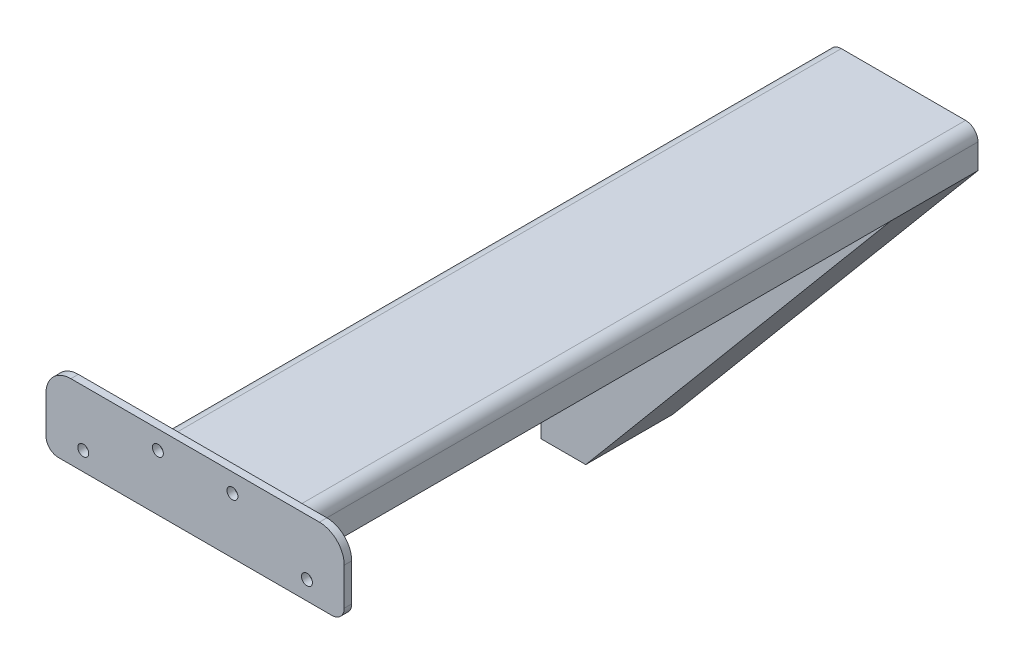
SolidWorks part; units mm, degrees
ref_plane "Front Plane" through (0, 0, 0) normal (0, 0, 1) x (1, 0, 0)
ref_plane "Top Plane" through (0, 0, 0) normal (0, 1, 0) x (1, 0, 0)
ref_plane "Right Plane" through (0, 0, 0) normal (1, 0, 0) x (0, 0, -1)
sketch "Sketch1" plane through (0, 0, 0) normal (0, 0, 1) x (1, 0, 0)
  line L23 (39.2356, -231.8935) -> (39.2356, -281.8935)
  line L24 (124.2987, -130.5192) -> (39.2356, -231.8935)
  line L25 (57.2806, -281.8935) -> (184.2987, -130.5192)
  line L26 (184.2987, -130.5192) -> (124.2987, -130.5192)
  line L27 (39.2356, -281.8935) -> (57.2806, -281.8935)
extrude "Boss-Extrude1" add sketch "Sketch1" along normal blind 35
sketch "Sketch5" plane through (0, -130.5192, 0) normal (0, 1, 0) x (1, 0, 0)
  line L0 (124.2987, -35) -> (39.2356, -35) construction
  line L1 (124.2987, 0) -> (84.2987, 0)
  line L2 (124.2987, 0) -> (124.2987, -35)
  line L3 (124.2987, -35) -> (84.2987, -35)
  line L4 (84.2987, 0) -> (84.2987, -35)
  line L5 (184.2987, 0) -> (184.2987, -35)
  line L6 (184.2987, 0) -> (204.2987, 0)
  line L10 (184.2987, -35) -> (204.2987, -35)
  line L11 (204.2987, -35) -> (204.2987, 0)
  dimension "D1" = 20
  dimension "D2" = 40
extrude "Boss-Extrude4" add sketch "Sketch5" against normal blind 5
sketch "Sketch6" plane through (0, 0, 35) normal (0, 0, 1) x (1, 0, 0)
  line L4 (184.2987, -130.5192) -> (184.2987, -135.5192)
  line L5 (184.2987, -135.5192) -> (180.1032, -135.5192)
  line L6 (57.2806, -281.8935) -> (184.2987, -130.5192) construction
  line L7 (180.1032, -135.5192) -> (184.2987, -130.5192)
extrude "Boss-Extrude5" add sketch "Sketch6" against normal blind 35
sketch "Sketch7" plane through (39.2356, 0, 0) normal (-1, 0, 0) x (0, 0, 1)
  line L0 (0, -231.8935) -> (35, -281.8935)
  line L6 (0, -231.8935) -> (35, -231.8935)
  line L22 (0, -231.8935) -> (0, -281.8935)
  line L23 (0, -281.8935) -> (35, -281.8935)
  line L24 (35, -231.8935) -> (35, -281.8935)
  line L25 (0, -281.8935) -> (35, -231.8935)
  line L27 (21.9741, -266.9425) -> (25.6746, -264.2539)
  line L28 (25.6746, -264.2539) -> (27.9616, -260.2927)
  line L29 (27.9616, -260.2927) -> (28.4397, -255.7437)
  line L30 (28.4397, -255.7437) -> (27.0263, -251.3935)
  line L31 (27.0263, -251.3935) -> (23.9656, -247.9943)
  line L32 (23.9656, -247.9943) -> (19.787, -246.1339)
  line L33 (19.787, -246.1339) -> (15.213, -246.1339)
  line L34 (15.213, -246.1339) -> (11.0344, -247.9943)
  line L35 (11.0344, -247.9943) -> (7.9737, -251.3935)
  line L36 (7.9737, -251.3935) -> (6.5603, -255.7437)
  line L37 (6.5603, -255.7437) -> (7.0384, -260.2927)
  line L38 (7.0384, -260.2927) -> (9.3254, -264.2539)
  line L39 (9.3254, -264.2539) -> (13.0259, -266.9425)
  line L40 (13.0259, -266.9425) -> (17.5, -267.8935)
  line L41 (17.5, -267.8935) -> (21.9741, -266.9425)
  circle A0 centre (17.5, -256.8935) radius 10.7596 construction
  dimension "D1" = 11
extrude "Cut-Extrude2" cut sketch "Sketch7" against normal blind 15
sketch "Sketch8" plane through (0, -135.5192, 0) normal (0, -1, 0) x (1, 0, 0)
  line L6 (180.1032, 35) -> (204.2987, 0)
  line L15 (84.2987, 35) -> (120.1032, 35)
  line L16 (84.2987, 35) -> (84.2987, 0)
  line L17 (84.2987, 0) -> (120.1032, 0)
  line L18 (120.1032, 35) -> (120.1032, 0)
  line L19 (180.1032, 35) -> (204.2987, 35)
  line L20 (180.1032, 35) -> (180.1032, 0)
  line L21 (180.1032, 0) -> (204.2987, 0)
  line L22 (204.2987, 35) -> (204.2987, 0)
  line L23 (204.2987, 35) -> (180.1032, 0)
  line L24 (84.2987, 35) -> (120.1032, 0)
  line L25 (120.1032, 35) -> (84.2987, 0)
  circle A4 centre (102.2009, 17.5) radius 2.15
  circle A5 centre (192.2009, 17.5) radius 2.15
  dimension "D1" = 4.3
  dimension "D2" = 4.3
extrude "Cut-Extrude3" cut sketch "Sketch8" against normal blind 10 contours L25 A4 L24 | L24 A4 L25 | L25 A4 L24 | L24 A4 L25 | L6 A5 L23 | L6 A5 L23 | L23 A5 L6 | L23 A5 L6
sketch "Sketch9" plane through (0, 0, 0) normal (0, 0, -1) x (-1, 0, 0)
  line L0 (-180.1032, -135.5192) -> (-180.1032, -120.5192)
  line L1 (-180.1032, -135.5192) -> (-120.1032, -135.5192)
  line L2 (-120.1032, -135.5192) -> (-120.1032, -120.5192)
  line L3 (-120.1032, -120.5192) -> (-180.1032, -120.5192)
  dimension "D1" = 15
extrude "Boss-Extrude6" add sketch "Sketch9" against normal blind 285
sketch "Sketch10" plane through (180.1032, 0, 0) normal (1, 0, 0) x (0, 0, -1)
  line L1 (-35, -130.5192) -> (0, -130.5192)
  line L2 (-35, -130.5192) -> (-35, -135.5192)
  line L3 (-35, -135.5192) -> (0, -135.5192)
  line L4 (0, -130.5192) -> (0, -135.5192)
extrude "Cut-Extrude4" cut sketch "Sketch10" along normal blind 250
sketch "Sketch11" plane through (120.1032, 0, 0) normal (-1, 0, 0) x (0, 0, 1)
  line L1 (0, -130.5192) -> (35, -130.5192)
  line L2 (0, -130.5192) -> (0, -135.5192)
  line L3 (0, -135.5192) -> (35, -135.5192)
  line L4 (35, -130.5192) -> (35, -135.5192)
extrude "Cut-Extrude5" cut sketch "Sketch11" along normal blind 250
sketch "Sketch12" plane through (0, 0, 285) normal (0, 0, 1) x (1, 0, 0)
  line L9 (120.1032, -120.5192) -> (90.1032, -120.5192)
  line L10 (120.1032, -120.5192) -> (120.1032, -135.5192)
  line L11 (120.1032, -135.5192) -> (90.1032, -135.5192)
  line L12 (90.1032, -120.5192) -> (90.1032, -135.5192)
  line L13 (180.1032, -120.5192) -> (210.1032, -120.5192)
  line L14 (180.1032, -120.5192) -> (180.1032, -135.5192)
  line L15 (180.1032, -135.5192) -> (210.1032, -135.5192)
  line L16 (210.1032, -120.5192) -> (210.1032, -135.5192)
  dimension "D1" = 30
  dimension "D2" = 30
extrude "Boss-Extrude7" add sketch "Sketch12" against normal blind 3
fillet "Fillet1" radius 5 1 edges at (120.1032, -135.5192, 17.5)
fillet "Fillet2" radius 5 2 edges at (180.1032, -120.5192, 141) (120.1032, -120.5192, 141)
sketch "Sketch13" plane through (0, 0, 282) normal (0, 0, -1) x (-1, 0, 0)
  line L0 (-180.1032, -135.5192) -> (-180.1032, -120.5192)
  line L1 (-210.1032, -120.5192) -> (-175.1032, -120.5192) construction
  line L2 (-210.1032, -120.5192) -> (-180.1032, -120.5192)
  line L3 (-120.1032, -135.5192) -> (-120.1032, -120.5192)
  line L4 (-125.1032, -120.5192) -> (-90.1032, -120.5192) construction
  line L5 (-120.1032, -120.5192) -> (-90.1032, -120.5192)
  circle A2 centre (-195.1032, -128.0192) radius 2.2
  circle A3 centre (-105.1032, -128.0192) radius 2.2
  dimension "D1" = 4.4
  dimension "D2" = 4.4
extrude "Cut-Extrude6" cut sketch "Sketch13" against normal blind 10 contours A3 | A2
sketch "Sketch15" plane through (0, 0, 282) normal (0, 0, -1) x (-1, 0, 0)
  line L1 (-210.1032, -120.5192) -> (-90.1032, -120.5192)
  line L2 (-210.1032, -120.5192) -> (-210.1032, -105.5192)
  line L3 (-210.1032, -105.5192) -> (-90.1032, -105.5192)
  line L4 (-90.1032, -120.5192) -> (-90.1032, -105.5192)
  dimension "D1" = 15
extrude "Boss-Extrude8" add sketch "Sketch15" against normal blind 3
sketch "Sketch16" plane through (0, 0, 282) normal (0, 0, -1) x (-1, 0, 0)
  line L0 (-180.1032, -135.5192) -> (-180.1032, -105.5192)
  line L1 (-90.1032, -105.5192) -> (-210.1032, -105.5192) construction
  line L2 (-120.1032, -135.5192) -> (-120.1032, -105.5192)
  line L3 (-150.1032, -105.5192) -> (-120.1032, -105.5192)
  line L4 (-210.1032, -120.5192) -> (-90.1032, -120.5192)
  line L5 (-210.1032, -135.5192) -> (-210.1032, -105.5192) construction
  line L6 (-90.1032, -105.5192) -> (-90.1032, -135.5192) construction
  line L8 (-120.1032, -120.5192) -> (-120.1032, -105.5192)
  line L9 (-150.1032, -105.5192) -> (-120.1032, -105.5192)
  line L10 (-150.1032, -105.5192) -> (-150.1032, -120.5192)
  circle A0 centre (-165.1032, -113.0192) radius 2.2
  circle A1 centre (-135.1032, -113.0192) radius 2.2
  dimension "D1" = 4.4
  dimension "D2" = 4.4
extrude "Cut-Extrude7" cut sketch "Sketch16" against normal blind 5 contours A0 | A1
fillet "Fillet3" radius 10 2 edges at (90.1032, -105.5192, 283.5) (210.1032, -105.5192, 283.5)
fillet "Fillet4" radius 5 2 edges at (210.1032, -135.5192, 283.5) (90.1032, -135.5192, 283.5)
